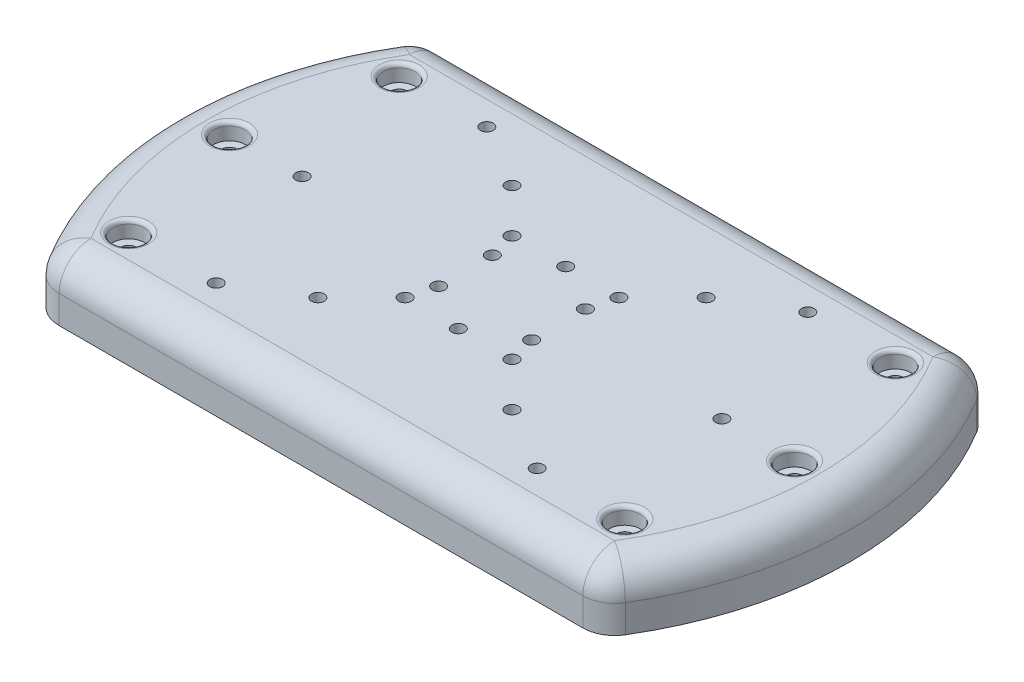
SolidWorks part; units mm, degrees
material "1060 合金"
ref_plane "前视基准面" through (0, 0, 0) normal (0, 0, 1) x (1, 0, 0)
ref_plane "上视基准面" through (0, 0, 0) normal (0, 1, 0) x (1, 0, 0)
ref_plane "右视基准面" through (0, 0, 0) normal (1, 0, 0) x (0, 0, -1)
other "Configuration Table"
sketch "草图1" plane through (0, 0, 0) normal (0, 1, 0) x (1, 0, 0)
  line L0 (0, 48) -> (49.2882, 48) construction
  line L1 (0, 13.5) -> (-11.6913, 6.75) construction
  line L2 (-11.6913, 6.75) -> (-11.6913, -6.75) construction
  line L3 (-11.6913, -6.75) -> (0, -13.5) construction
  line L4 (0, -13.5) -> (11.6913, -6.75) construction
  line L5 (11.6913, -6.75) -> (11.6913, 6.75) construction
  line L6 (11.6913, 6.75) -> (0, 13.5) construction
  line L7 (0, -48) -> (39.2438, -48) construction
  line L8 (0, 40) -> (-53.007, 40) construction
  line L9 (0, -40) -> (-54.5432, -40) construction
  line L10 (0, 34) -> (-53.007, 34) construction
  line L11 (-55, 0) -> (55, 0) construction
  line L12 (0, -34) -> (-53.007, -34) construction
  line L13 (-70.1498, 48) -> (70.1498, 48)
  line L14 (-70.1498, -48) -> (70.1498, -48)
  line L15 (0, 0) -> (23.2549, 23.2549) construction
  line L16 (0, 0) -> (-7.965, 7.965) construction
  circle A0 centre (0, 0) radius 13.5 construction
  circle A1 centre (0, 13.5) radius 1.6
  circle A2 centre (-11.6913, 6.75) radius 1.6
  circle A3 centre (11.6913, 6.75) radius 1.6
  circle A4 centre (11.6913, -6.75) radius 1.6
  circle A5 centre (-11.6913, -6.75) radius 1.6
  circle A6 centre (0, -13.5) radius 1.6
  circle A7 centre (0, 0) radius 40 construction
  circle A8 centre (0, 0) radius 48 construction
  circle A9 centre (0, 0) radius 85 construction
  circle A10 centre (0, 0) radius 77 construction
  circle A11 centre (0, 0) radius 71 construction
  arc A12 (70.1498, 48) -> (70.1498, -48) centre (0, 0) cw
  arc A13 (-70.1498, 48) -> (-70.1498, -48) centre (0, 0) ccw
  circle A14 centre (-62.3424, 34) radius 2
  circle A15 centre (-71, 0) radius 2
  circle A16 centre (-62.3298, -34) radius 2
  circle A18 centre (71, 0) radius 2
  circle A19 centre (62.3298, -34) radius 2
  circle A20 centre (0, 0) radius 28.5 construction
  circle A21 centre (62.3298, 34) radius 2
  circle A22 centre (0, 0) radius 34.5 construction
  circle A28 centre (-24.3952, 24.3952) radius 1.6
  circle A29 centre (24.3952, 24.3952) radius 1.6
  circle A30 centre (24.3952, -24.3952) radius 1.6
  circle A31 centre (-24.3952, -24.3952) radius 1.6
  circle A32 centre (0, 0) radius 19 construction
  circle A33 centre (13.435, 13.435) radius 1.6
  circle A34 centre (-13.435, 13.435) radius 1.6
  circle A35 centre (-13.435, -13.435) radius 1.6
  circle A36 centre (13.435, -13.435) radius 1.6
  circle A37 centre (0, 0) radius 52.75 construction
  circle A38 centre (-40.3307, 34) radius 1.6
  circle A39 centre (-52.75, 0) radius 1.6
  circle A40 centre (-40.3307, -34) radius 1.6
  circle A41 centre (40.3307, 34) radius 1.6
  circle A42 centre (52.75, 0) radius 1.6
  circle A43 centre (40.3307, -34) radius 1.6
  dimension "D1" = 6
extrude "凸台-拉伸1" add sketch "草图1" along normal blind 15
fillet "圆角1" radius 8 8 edges at (85, 15, 0) (0, 15, -48) (-85, 15, 0) (0, 15, 48) (-70.1498, 7.5, -48) (70.1498, 7.5, -48) (70.1498, 7.5, 48) (-70.1498, 7.5, 48)
sketch "草图2" plane through (0, 15, 0) normal (0, 1, 0) x (1, 0, 0)
  circle A0 centre (-62.3424, 34) radius 4
  circle A1 centre (-71, 0) radius 4
  circle A2 centre (-62.3298, -34) radius 4
  circle A3 centre (62.3298, 34) radius 4
  circle A4 centre (71, 0) radius 4
  circle A5 centre (62.3298, -34) radius 4
extrude "切除-拉伸1" cut sketch "草图2" against normal blind 4.2
sketch "草图3" plane through (0, 0, 0) normal (0, -1, 0) x (1, 0, 0)
  line L0 (-17.9047, 17.496) -> (-14.3635, 3.9198) construction
  line L1 (-11.6085, 19.5073) -> (-7.1971, 2.5947) construction
  line L2 (-16.6282, 12.6021) -> (-14.8845, 5.9171)
  line L3 (-10.2419, 14.2679) -> (-8.4982, 7.5829)
  line L4 (0, -55) -> (0, 55) construction
  line L5 (10.2419, 14.2679) -> (8.4982, 7.5829)
  line L6 (16.6282, 12.6021) -> (14.8845, 5.9171)
  line L7 (55, 0) -> (-55, 0) construction
  line L8 (16.6282, -12.6021) -> (14.8845, -5.9171)
  line L9 (10.2419, -14.2679) -> (8.4982, -7.5829)
  line L10 (-10.2419, -14.2679) -> (-8.4982, -7.5829)
  line L11 (-16.6282, -12.6021) -> (-14.8845, -5.9171)
  circle A0 centre (0, 13.5) radius 3.3
  circle A1 centre (-24.3952, 24.3952) radius 3.3
  circle A2 centre (-11.6913, 6.75) radius 3.3 construction
  circle A4 centre (-24.3952, -24.3952) radius 3.3
  circle A6 centre (0, -13.5) radius 3.3
  circle A8 centre (24.3952, -24.3952) radius 3.3
  circle A10 centre (24.3952, 24.3952) radius 3.3
  circle A11 centre (-13.435, 13.435) radius 3.3 construction
  arc A12 (-16.6282, 12.6021) -> (-10.2419, 14.2679) centre (-13.435, 13.435) cw
  arc A13 (-14.8845, 5.9171) -> (-8.4982, 7.5829) centre (-11.6913, 6.75) ccw
  arc A14 (14.8845, 5.9171) -> (8.4982, 7.5829) centre (11.6913, 6.75) cw
  arc A15 (16.6282, 12.6021) -> (10.2419, 14.2679) centre (13.435, 13.435) ccw
  arc A16 (16.6282, -12.6021) -> (10.2419, -14.2679) centre (13.435, -13.435) cw
  arc A17 (14.8845, -5.9171) -> (8.4982, -7.5829) centre (11.6913, -6.75) ccw
  arc A18 (-14.8845, -5.9171) -> (-8.4982, -7.5829) centre (-11.6913, -6.75) cw
  arc A19 (-16.6282, -12.6021) -> (-10.2419, -14.2679) centre (-13.435, -13.435) ccw
  circle A20 centre (-40.3307, 34) radius 3.3
  circle A21 centre (-52.75, 0) radius 3.3
  circle A22 centre (-40.3307, -34) radius 3.3
  circle A23 centre (40.3307, 34) radius 3.3
  circle A24 centre (52.75, 0) radius 3.3
  circle A25 centre (40.3307, -34) radius 3.3
extrude "切除-拉伸2" cut sketch "草图3" against normal blind 3.2
fillet "圆角2" radius 1 34 edges at (62.3298, 15, 38) (71, 15, 4) (62.3298, 15, -30) (-62.3298, 15, 38) (-71, 15, 4) (-62.3424, 15, -30) (24.3952, 0, -27.6952) (24.3952, 0, 21.0952) (0, 0, 10.2) (0, 0, -16.8) (-24.3952, 0, -27.6952) (-24.3952, 0, 21.0952) (10.8585, 0, -3.5568) (15.7564, 0, -9.2596) (14.2679, 0, -16.6282) (-14.2679, 0, -16.6282) (-15.7564, 0, -9.2596) (-10.8585, 0, -3.5568) (14.2679, 0, 16.6282) (15.7564, 0, 9.2596) (10.8585, 0, 3.5568) (-10.8585, 0, 3.5568) (-15.7564, 0, 9.2596) (-14.2679, 0, 16.6282) (9.37, 0, -10.9254) (-9.37, 0, -10.9254) (9.37, 0, 10.9254) (-9.37, 0, 10.9254) (-40.3307, 0, 30.7) (-52.75, 0, -3.3) (-40.3307, 0, -37.3) (40.3307, 0, -37.3) (52.75, 0, -3.3) (40.3307, 0, 30.7)
